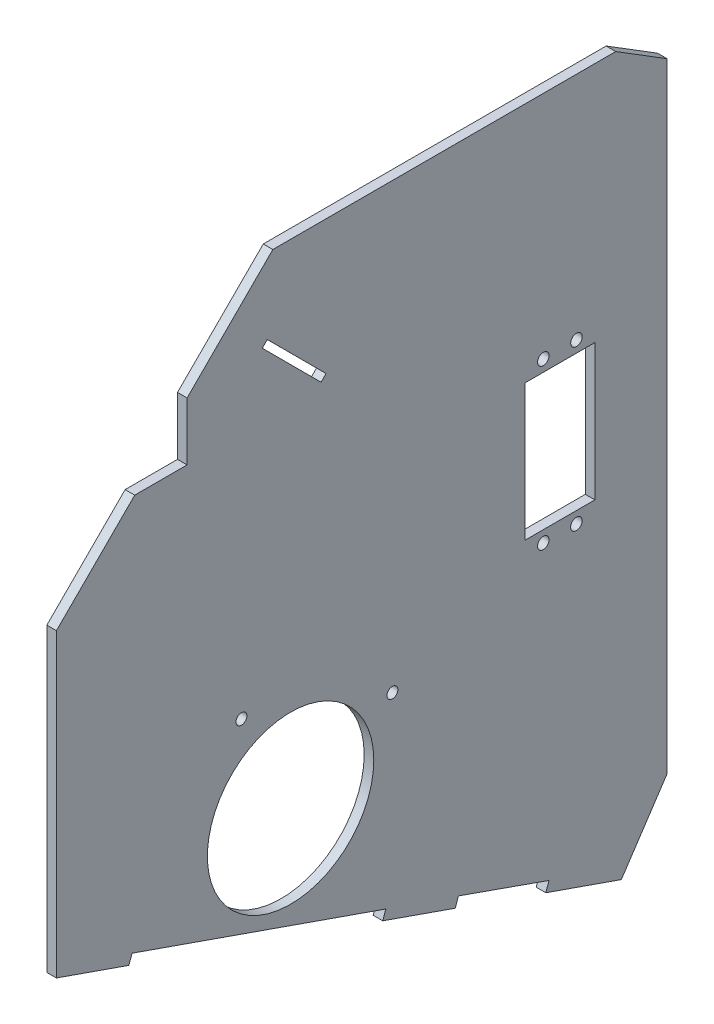
SolidWorks part; units mm, degrees
ref_plane "Front Plane" through (0, 0, 0) normal (0, 0, 1) x (1, 0, 0)
ref_plane "Top Plane" through (0, 0, 0) normal (0, 1, 0) x (1, 0, 0)
ref_plane "Right Plane" through (0, 0, 0) normal (1, 0, 0) x (0, 0, -1)
sketch "Sketch1" plane through (0, 0, 0) normal (1, 0, 0) x (0, 0, -1)
  line L38 (-110.8824, -2.7312) -> (-88.2232, -10.643)
  line L74 (-88.2232, -10.643) -> (-87.2342, -7.8107)
  line L86 (-189.2359, 27.6834) -> (-109.9313, -0.0072)
  line L89 (-109.9313, -0.0072) -> (-110.8824, -2.7312)
  line L90 (-212.8713, 32.7972) -> (-190.2128, 24.8856)
  line L91 (-190.2128, 24.8856) -> (-189.2359, 27.6834)
  line L99 (-149.5836, 13.8381) -> (-131.4529, 65.7637) construction
  line L100 (-188.3982, 151.2445) -> (-212.8713, 126.7979)
  line L104 (-172.0362, 169.3662) -> (-172.0362, 151.2445)
  line L105 (-172.0362, 169.3662) -> (-145.2305, 196.1428)
  line L106 (-99.5528, -6.6871) -> (-73.9817, 66.5473) construction
  line L107 (-172.0362, 151.2445) -> (-188.3982, 151.2445)
  line L109 (-155.04, 73.9996) -> (-107.8657, 57.5279) construction
  line L111 (-212.8713, 32.7972) -> (-212.8713, 126.7979)
  line L130 (-38.0834, 196.1428) -> (-145.2305, 196.1428)
  line L132 (-158.6333, 182.7545) -> (-133.6121, 157.7061) construction
  line L133 (-148.5351, 171.0818) -> (-146.9716, 172.6436)
  line L134 (-148.5351, 171.0818) -> (-130.1603, 152.687)
  line L135 (-146.9716, 172.6436) -> (-128.5968, 154.2488)
  line L136 (-128.5968, 154.2488) -> (-130.1603, 152.687)
  line L137 (-87.2342, -7.8107) -> (-58.9376, -17.7738)
  line L139 (-36.324, -28.8473) -> (-22.0034, -7.3227)
  line L140 (-22.0034, -7.3227) -> (-22.0034, 186.1647)
  line L141 (-38.0834, 196.1428) -> (-22.0034, 186.1647)
  line L142 (-58.9376, -17.7738) -> (-59.9266, -20.6061)
  line L143 (-59.9266, -20.6061) -> (-36.324, -28.8473)
  line L148 (-60.6979, 124.2516) -> (-50.3479, 124.2473) construction
  line L154 (-60.7183, 74.4516) -> (-50.3683, 74.4474) construction
  line L155 (-50.3683, 74.4474) -> (-55.5433, 74.4495) construction
  line L156 (-55.5433, 74.4495) -> (-55.5229, 124.2495) construction
  line L158 (-66.4722, 78.0601) -> (-44.594, 78.0601)
  line L159 (-66.4722, 78.0601) -> (-66.4722, 120.6389)
  line L160 (-66.4722, 120.6389) -> (-44.594, 120.6389)
  line L161 (-44.594, 78.0601) -> (-44.594, 120.6389)
  line L162 (-66.4722, 78.0601) -> (-44.594, 120.6389) construction
  line L163 (-66.4722, 120.6389) -> (-44.594, 78.0601) construction
  circle A6 centre (-155.04, 73.9996) radius 1.7
  circle A8 centre (-107.8657, 57.5279) radius 1.7
  circle A15 centre (-139.6941, 42.1612) radius 26
  circle A20 centre (-60.7183, 74.4516) radius 1.8
  circle A21 centre (-50.3683, 74.4474) radius 1.8
  circle A22 centre (-60.6979, 124.2516) radius 1.8
  circle A23 centre (-50.3479, 124.2473) radius 1.8
  point P34 (-55.5331, 99.3495)
  point P40 (-147.7533, 171.8627)
  dimension "D3" = 49.9673
  dimension "D1" = 24
  dimension "D2" = 55
  dimension "D4" = 30
  dimension "D5" = 84
extrude "Boss-Extrude1" add sketch "Sketch1" along normal blind 3
